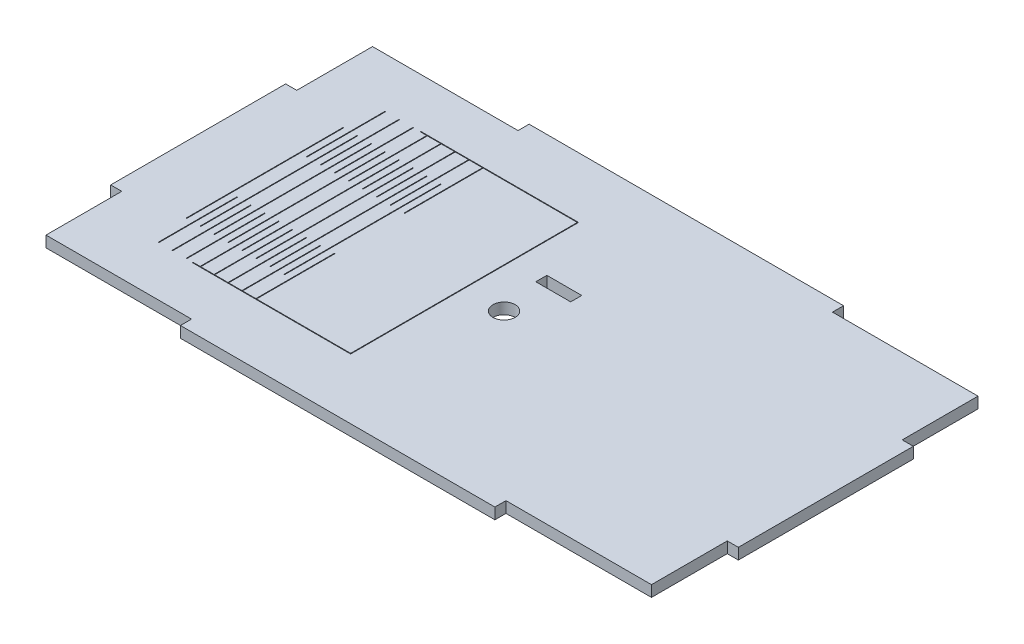
SolidWorks part; units mm, degrees
ref_plane "Front Plane" through (0, 0, 0) normal (0, 0, 1) x (1, 0, 0)
ref_plane "Top Plane" through (0, 0, 0) normal (0, 1, 0) x (1, 0, 0)
ref_plane "Right Plane" through (0, 0, 0) normal (1, 0, 0) x (0, 0, -1)
sketch "Sketch1" plane through (0, 0, 0) normal (0, 1, 0) x (1, 0, 0)
  line L0 (0, 50) -> (0, -50) construction
  line L1 (90, 50) -> (-90, 50)
  line L2 (90, 50) -> (90, -50)
  line L3 (90, -50) -> (-90, -50)
  line L4 (-90, 50) -> (-90, -50)
  line L5 (-90, 0) -> (90, 0) construction
  point P8 (0, 0)
  dimension "D1" = 180
  dimension "D2" = 100
extrude "Boss-Extrude1" add sketch "Sketch1" along normal blind 3.18
sketch "Sketch3" plane through (0, 3.18, 0) normal (0, 1, 0) x (1, 0, 0)
  line L1 (90, -50) -> (45.09, -50)
  line L2 (90, -50) -> (90, -46.82)
  line L3 (90, -46.82) -> (45.09, -46.82)
  line L4 (45.09, -50) -> (45.09, -46.82)
  dimension "D1" = 3.18
  dimension "D2" = 44.91
extrude "Cut-Extrude1" cut sketch "Sketch3" against normal up to surface (3.18 mm away) up to face at (0, 0, 0)
mirror "Mirror1" about plane through (0, 0, 0) normal (1, 0, 0) of "Cut-Extrude1"
mirror "Mirror2" about plane through (0, 0, 0) normal (0, 0, 1) of "Mirror1", "Cut-Extrude1"
sketch "Sketch4" plane through (0, 3.18, 0) normal (0, 1, 0) x (1, 0, 0)
  line L6 (-45.09, 50) -> (-93.6365, 50) construction
  line L7 (-90, 46.82) -> (-90, -46.82) construction
  line L8 (-86.82, 50) -> (-90, 50)
  line L9 (-86.82, 50) -> (-86.82, 25.09)
  line L10 (-86.82, 25.09) -> (-90, 25.09)
  line L11 (-90, 50) -> (-90, 25.09)
  dimension "D1" = 3.18
  dimension "D2" = 24.91
extrude "Cut-Extrude2" cut sketch "Sketch4" against normal up to surface (3.18 mm away) up to face at (0, 0, 0)
mirror "Mirror3" about plane through (0, 0, 0) normal (0, 0, 1) of "Cut-Extrude2"
mirror "Mirror4" about plane through (0, 0, 0) normal (1, 0, 0) of "Mirror3", "Cut-Extrude2"
sketch "Sketch5" plane through (0, 3.18, 0) normal (0, 1, 0) x (1, 0, 0)
  line L1 (-58.7712, 22.5) -> (-58.7712, -22.5)
  line L2 (-56.7712, 32.5) -> (-56.7712, 10)
  line L4 (0, 0) -> (-90, 0) construction
  line L5 (-90, 25.09) -> (-90, -25.09) construction
  line L8 (-56.7712, -10) -> (-56.7712, -32.5)
  line L11 (-86.82, 46.82) -> (-45.09, 46.82) construction
  line L13 (-56.7712, 32.5) -> (-56.7712, 46.82) construction
  line L14 (-56.7712, -32.5) -> (-56.7712, -46.82) construction
  line L15 (-86.82, -46.82) -> (-45.09, -46.82) construction
  dimension "D1" = 2
  dimension "D2" = 22.5
  dimension "D3" = 31.2288
  dimension "D4" = 24.32
  dimension "D5" = 24.32
  dimension "D6" = 10
  dimension "D7" = 45
sketch "Sketch6" plane through (0, 3.18, 0) normal (0, 1, 0) x (1, 0, 0)
  line L1 (-45.09, -50) -> (45.09, -50) construction
  line L2 (-90, 25.09) -> (-90, -25.09) construction
  circle A0 centre (-2.2712, 0) radius 3.18
  point P7 (0, -50)
  dimension "D1" = 6.36
  dimension "D2" = 87.7288
  dimension "D3" = 50
extrude "Cut-Extrude3" cut sketch "Sketch6" against normal up to surface (3.18 mm away) up to face at (0, 0, 0)
sketch "Sketch7" plane through (0, 3.18, 0) normal (0, 1, 0) x (1, 0, 0)
  line L1 (-5, 11.82) -> (5, 11.82)
  line L2 (-5, 11.82) -> (-5, 15)
  line L3 (-5, 15) -> (5, 15)
  line L4 (5, 11.82) -> (5, 15)
  line L6 (45.09, 50) -> (-45.09, 50) construction
  line L7 (-90, 25.09) -> (-90, -25.09) construction
  dimension "D1" = 3.18
  dimension "D2" = 10
  dimension "D3" = 35
  dimension "D4" = 85
extrude "Cut-Extrude4" cut sketch "Sketch7" against normal up to surface (3.18 mm away) up to face at (-2.2712, 0, -3.18)
sketch "Sketch8" plane through (0, 3.18, 0) normal (0, 1, 0) x (1, 0, 0)
  line L1 (-75, -30) -> (-35, -30)
  line L2 (-75, -30) -> (-75, 30)
  line L3 (-75, 30) -> (-35, 30)
  line L4 (-35, -30) -> (-35, 30)
  line L6 (-90, 25.09) -> (-90, -25.09) construction
  line L7 (90, -25.09) -> (90, 25.09) construction
  line L8 (-45.09, -50) -> (45.09, -50) construction
  line L9 (45.09, 50) -> (-45.09, 50) construction
  dimension "D1" = 60
  dimension "D2" = 40
  dimension "D3" = 20
  dimension "D4" = 20
  dimension "D5" = 15
  dimension "D6" = 125
extrude "Cut-Extrude5" [suppressed] cut sketch "Sketch8" against normal through all
extrude "Cut-Extrude-Thin1" cut sketch "Sketch5" against normal blind 10 thin
pattern_linear "LPattern2" count 5 spacing 4 along (0.0937, 0, 0.9956) count 4 spacing 4 along (-0.0937, 0, 0.9956) of "Cut-Extrude-Thin1"
sketch "Sketch9" plane through (0, 3.18, 0) normal (0, 1, 0) x (1, 0, 0)
  line L0 (-58.7712, 22.5) -> (-58.7712, 32.5) construction
  line L1 (-58.7712, 32.5) -> (-13.7712, 32.5)
  line L2 (-13.7712, 32.5) -> (-13.7712, -32.5)
  line L3 (-58.9512, -22.5) -> (-58.9512, -32.5) construction
  line L4 (-58.9512, -32.5) -> (-13.7712, -32.5)
  line L5 (-58.7712, 22.5) -> (-58.7712, -22.5) construction
  line L6 (-90, 25.09) -> (-90, -25.09) construction
  point P10 (-13.7712, 0)
  point P13 (-90, 0)
  dimension "D1" = 45
  dimension "D2" = 65
extrude "Cut-Extrude-Thin2" cut sketch "Sketch9" against normal blind 10 and the other way through all thin thin type one direction wall 0.18
equation "\"h\"= 100"
equation "\"w\"= 100"
equation "\"l\"= 180"
equation "\"kerf\"= .18"
equation "\"tablen\"= \"h\" / 2"
equation "\"D1@Sketch1\"=\"l\""
equation "\"D2@Sketch1\"=\"w\""
equation "\"D2@Sketch3\"=45-\"kerf\"/2"
equation "\"D2@Sketch4\"=25-\"kerf\"/2"
equation "\"nLines\"= 6"
equation "\"nSmallLines\"= \"nLines\" - 1"
equation "\"D1@LPattern2\"=\"nLines\"/2+1"
equation "\"nLines\"= 8"
equation "\"D2@LPattern2\"=\"nLines\"/2"
equation "\"linesDist\"= 4"
